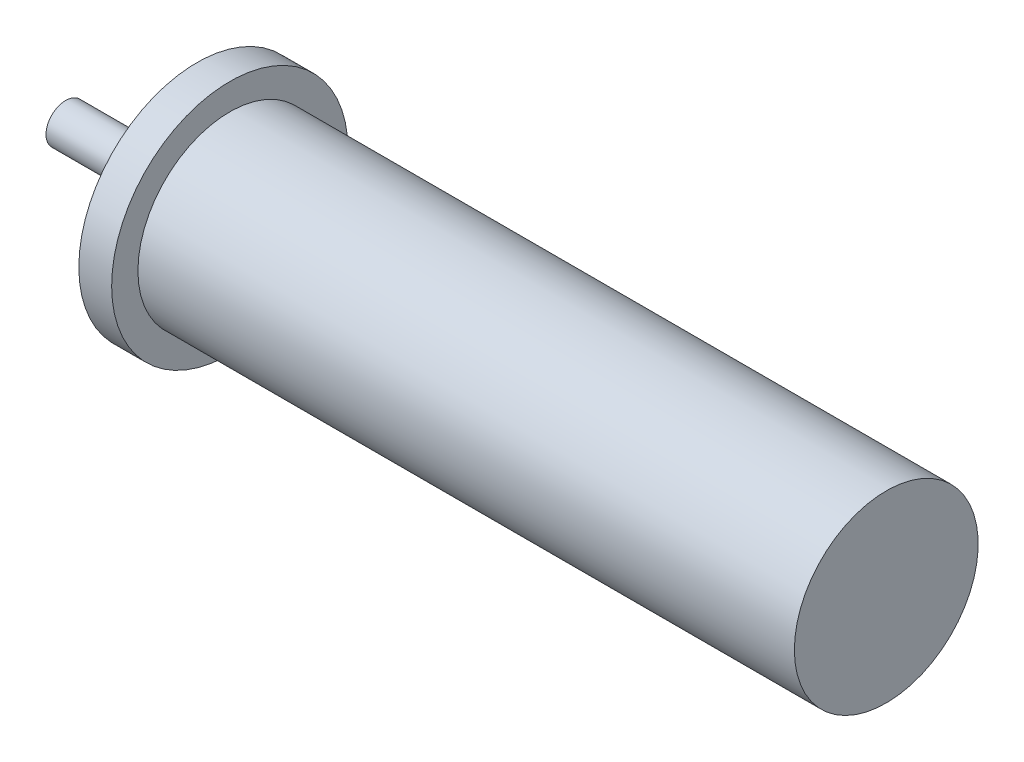
SolidWorks part; units mm, degrees
ref_plane "Front Plane" through (0, 0, 0) normal (0, 0, 1) x (1, 0, 0)
ref_plane "Top Plane" through (0, 0, 0) normal (0, 1, 0) x (1, 0, 0)
ref_plane "Right Plane" through (0, 0, 0) normal (1, 0, 0) x (0, 0, -1)
sketch "Sketch1" plane through (0, 0, 0) normal (0, 0, 1) x (1, 0, 0)
  line L0 (0, -3) -> (0, 3)
  line L5 (0, 3) -> (18, 3)
  line L6 (18, 3) -> (18, 11)
  line L7 (18, 11) -> (20, 11)
  line L8 (20, 11) -> (20, 18)
  line L9 (20, 18) -> (25, 18)
  line L10 (25, 18) -> (25, 14)
  line L11 (25, 14) -> (125, 14)
  line L12 (125, 14) -> (125, -14)
  line L13 (68.75, 0) -> (-68.75, 0) construction
  line L14 (25, -14) -> (125, -14)
  line L15 (25, -18) -> (25, -14)
  line L16 (20, -18) -> (25, -18)
  line L17 (20, -11) -> (20, -18)
  line L18 (18, -11) -> (20, -11)
  line L19 (18, -3) -> (18, -11)
  line L20 (0, -3) -> (18, -3)
  line L21 (0, 0) -> (125, 0)
  point P15 (125, 0)
  point P22 (0, 0)
  dimension "D1" = 6
  dimension "D2" = 22
  dimension "D3" = 36
  dimension "D4" = 5
  dimension "D5" = 2
  dimension "D6" = 18
  dimension "D7" = 105
  dimension "D8" = 28
revolve "Revolve1" add sketch "Sketch1" angle 360 about L21
